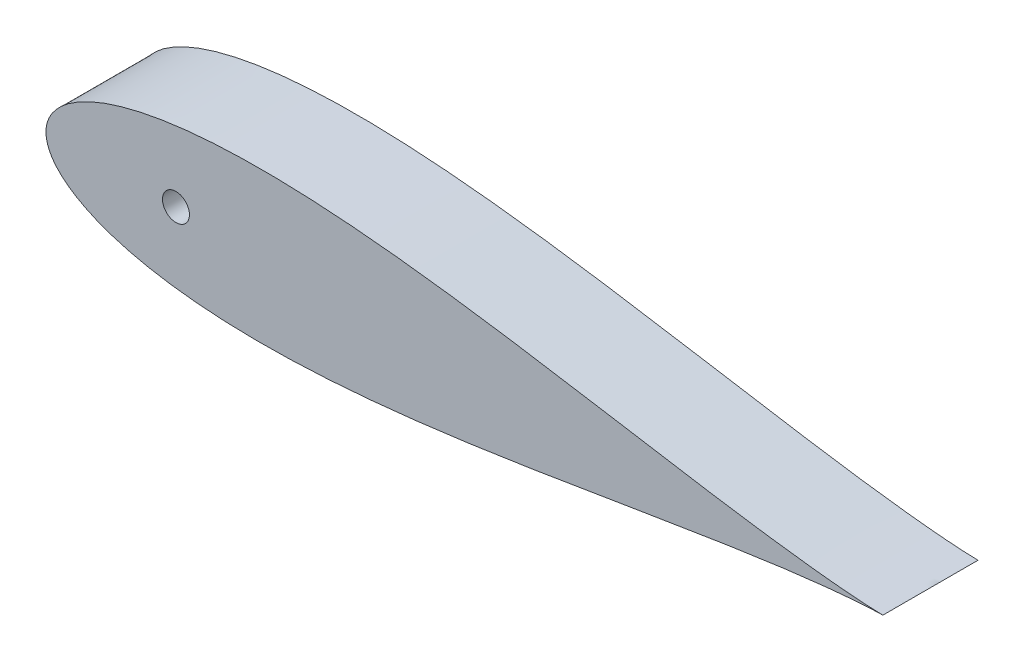
SolidWorks part; units mm, degrees
ref_plane "Front Plane" through (0, 0, 0) normal (0, 0, 1) x (1, 0, 0)
ref_plane "Top Plane" through (0, 0, 0) normal (0, 1, 0) x (1, 0, 0)
ref_plane "Right Plane" through (0, 0, 0) normal (1, 0, 0) x (0, 0, -1)
sketch "Sketch1" plane through (0, 0, 0) normal (0, 0, 1) x (1, 0, 0)
  line L0 (100, 0) -> (0, 0) construction
  line L1 (1.2169, -991.9959) -> (1.2169, 49008.0041) construction
  line L2 (93.345, 0) -> (114.935, 0) construction
  line L3 (125.634, 0) -> (131.6629, 0) construction
  line L4 (643.5991, 0) -> (643.5991, -1.016)
  line L9 (0, 0) -> (643.9668, 0)
  line L13 (460.661, 0) -> (473.361, 0)
  circle A0 centre (104.14, 0) radius 10.795 construction
  arc A1 (1.2169, -4.6585) -> (1.2169, 4.6585) centre (9.525, 0) cw
  arc A2 (641.5671, 0) -> (644.1071, 0) centre (642.8371, 0) ccw
  circle A4 centre (104.14, 0) radius 10.795
  circle A9 centre (40.64, 0) radius 12.7
  circle A14 centre (642.3793, 0) radius 1.5875 construction
  arc A15 (642.5108, -1.582) -> (642.5108, 1.582) centre (642.3793, 0) ccw
  spline S2 degree 3 poles (666.3448, -0.0547) (672.2538, 0) (666.3448, 0.0547) (662.8509, 0.2344) (656.505, 0.5436) (649.293, 1.0348) (640.4916, 1.7319) (630.4138, 2.6634) (619.0141, 3.8493) (606.375, 5.3044) (592.5439, 7.0376) (577.5855, 9.0506) (561.5643, 11.3389) (544.5497, 13.8907) (526.6141, 16.6877) (507.8326, 19.7051) (488.2827, 22.9117) (468.0444, 26.2704) (447.1994, 29.739) (425.8316, 33.2703) (404.0263, 36.8132) (381.8707, 40.3133) (359.4533, 43.7135) (336.8645, 46.9554) (314.1962, 49.9798) (291.5418, 52.7277) (268.9963, 55.1412) (246.6566, 57.1646) (224.6209, 58.7452) (202.9892, 59.8341) (181.8631, 60.3875) (161.3458, 60.367) (141.542, 59.7399) (122.5581, 58.4818) (104.5023, 56.5743) (87.485, 54.0089) (71.6197, 50.7848) (57.0237, 46.9125) (43.8205, 42.415) (32.1416, 37.3322) (22.1291, 31.7315) (13.9324, 25.7264) (7.6896, 19.5132) (3.4631, 13.4204) (1.1063, 7.9234) (0.1546, 3.5138) (-0.0622, 0) (0.1546, -3.5138) (1.1063, -7.9234) (3.4631, -13.4204) (7.6896, -19.5132) (13.9324, -25.7264) (22.1291, -31.7315) (32.1416, -37.3322) (43.8205, -42.415) (57.0237, -46.9125) (71.6197, -50.7848) (87.485, -54.0089) (104.5023, -56.5743) (122.5581, -58.4818) (141.542, -59.7399) (161.3458, -60.367) (181.8631, -60.3875) (202.9892, -59.8341) (224.6209, -58.7452) (246.6566, -57.1646) (268.9963, -55.1412) (291.5418, -52.7277) (314.1962, -49.9798) (336.8645, -46.9554) (359.4533, -43.7135) (381.8707, -40.3133) (404.0263, -36.8132) (425.8316, -33.2703) (447.1994, -29.739) (468.0444, -26.2704) (488.2827, -22.9117) (507.8326, -19.7051) (526.6141, -16.6877) (544.5497, -13.8907) (561.5643, -11.3389) (577.5855, -9.0506) (592.5439, -7.0376) (606.375, -5.3044) (619.0141, -3.8493) (630.4138, -2.6634) (640.4916, -1.7319) (649.293, -1.0348) (656.505, -0.5436) (662.8509, -0.2344) (666.3448, -0.0547) (672.2538, 0) (666.3448, 0.0547) knots -0.009667 -0.005395 -0.002168 0 0.002168 0.005395 0.009667 0.014967 0.021271 0.028553 0.036781 0.04592 0.055932 0.066773 0.078397 0.090755 0.103793 0.117456 0.131686 0.146422 0.1616 0.177156 0.193024 0.209135 0.225421 0.241812 0.258238 0.274629 0.290914 0.307025 0.322893 0.338448 0.353626 0.368361 0.38259 0.396253 0.40929 0.421647 0.43327 0.444109 0.454119 0.463255 0.471479 0.478755 0.485052 0.490344 0.49461 0.497833 0.5 0.502167 0.50539 0.509656 0.514948 0.521245 0.528521 0.536745 0.545881 0.555891 0.56673 0.578353 0.59071 0.603747 0.61741 0.631639 0.646374 0.661552 0.677107 0.692975 0.709086 0.725371 0.741762 0.758188 0.774579 0.790865 0.806976 0.822844 0.8384 0.853578 0.868314 0.882544 0.896207 0.909245 0.921603 0.933227 0.944068 0.95408 0.963219 0.971447 0.978729 0.985033 0.990333 0.994605 0.997832 1 1.002168 1.005395 1.009667 only from (670.56, 0) to (670.56, 0)
  point P2 (167.64, 0)
  point P8 (1.2169, -4.6585)
  point P10 (1.2169, 4.6585)
  point P28 (133.9182, 0)
  point P49 (130.0977, 0)
  point P59 (95.1064, 0)
  dimension "D2" = 21.59
  dimension "D3" = 1.016
  dimension "D4" = 1.27
  dimension "D8" = 25.4
  dimension "D9" = 63.5
  dimension "D10" = 3.175
  dimension "D6" = 63.5
extrude "Boss-Extrude1" add sketch "Sketch1" along normal blind 76.2 contours S2
sketch "Sketch3" plane through (0, 0, 76.2) normal (0, 0, 1) x (1, 0, 0)
  circle A0 centre (104.1392, 0) radius 10.795
  dimension "D1" = 21.59
extrude "Cut-Extrude2" cut sketch "Sketch3" against normal blind 76.2
sketch "Sketch4" plane through (0, 0, 76.2) normal (0, 0, 1) x (1, 0, 0)
sketch "Sketch6" plane through (0, 0, 0) normal (1, 0, 0) x (0, 0, -1)
  circle A0 centre (-20.32, 0) radius 6.35
  dimension "D1" = 12.7
  dimension "D2" = 20.32
extrude "Cut-Extrude3" cut sketch "Sketch6" against normal blind 0.0003 and the other way blind 53.34
